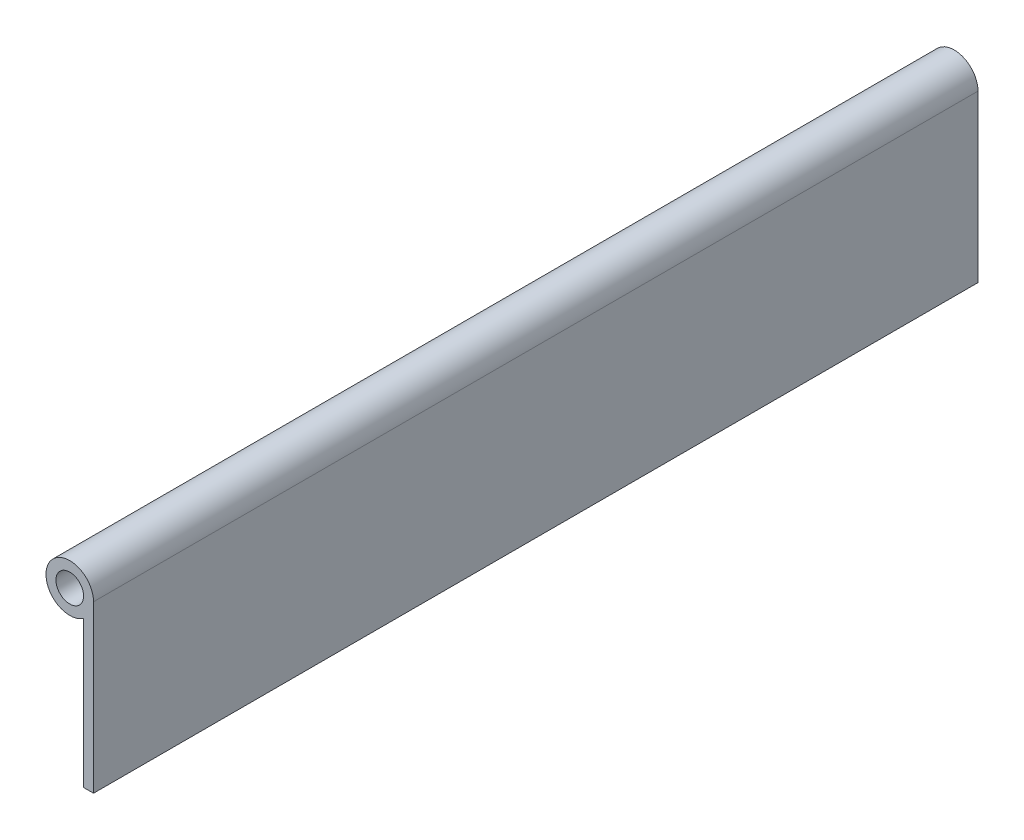
SolidWorks part; units mm, degrees
material "6061 Alloy"
ref_plane "Front Plane" through (0, 0, 0) normal (0, 0, 1) x (1, 0, 0)
ref_plane "Top Plane" through (0, 0, 0) normal (0, 1, 0) x (1, 0, 0)
ref_plane "Right Plane" through (0, 0, 0) normal (1, 0, 0) x (0, 0, -1)
sketch "Sketch1" plane through (0, 0, 0) normal (0, 0, 1) x (1, 0, 0)
  line L0 (5.461, 0) -> (5.461, -38.1)
  line L1 (5.461, -38.1) -> (3.175, -38.1)
  line L2 (3.175, -38.1) -> (3.175, -4.4432)
  circle A0 centre (0, 0) radius 3.175
  arc A1 (5.461, 0) -> (3.175, -4.4432) centre (0, 0) ccw
  circle A2 centre (0, 0) radius 5.461 construction
  dimension "D1" = 6.35
  dimension "D3" = 2.286
  dimension "D4" = 38.1
  dimension "D2" = 2.286
extrude "Boss-Extrude1" add sketch "Sketch1" along normal blind 203.2
sketch "Sketch2" plane through (5.461, 0, 0) normal (1, 0, 0) x (0, 0, -1)
  line L1 (-203.2, 5.461) -> (-177.8, 5.461)
  line L2 (-203.2, 5.461) -> (-203.2, -7.239)
  line L3 (-203.2, -7.239) -> (-177.8, -7.239)
  line L4 (-177.8, 5.461) -> (-177.8, -7.239)
  dimension "D1" = 12.7
  dimension "D2" = 25.4
extrude "Cut-Extrude1" [suppressed] cut sketch "Sketch2" against normal through all
pattern_linear "LPattern1" [suppressed] count 4 spacing 50.8
